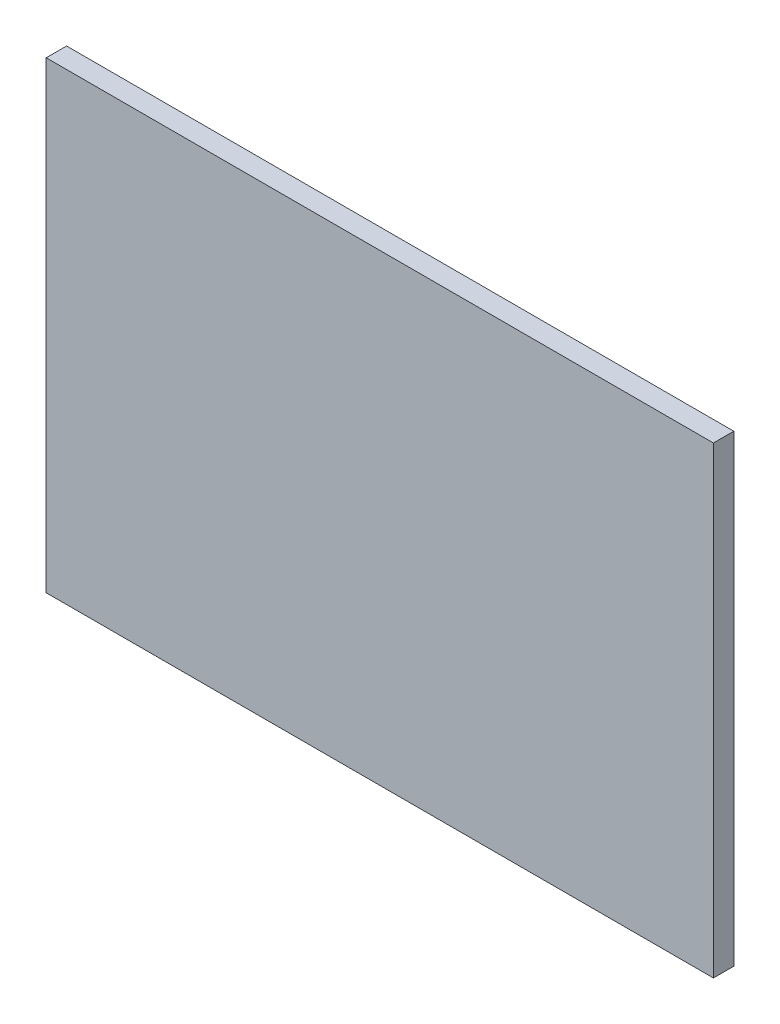
SolidWorks part; units mm, degrees
ref_plane "前视基准面" through (0, 0, 0) normal (0, 0, 1) x (1, 0, 0)
ref_plane "上视基准面" through (0, 0, 0) normal (0, 1, 0) x (1, 0, 0)
ref_plane "右视基准面" through (0, 0, 0) normal (1, 0, 0) x (0, 0, -1)
sketch "草图1" plane through (0, 0, 0) normal (0, 0, 1) x (1, 0, 0)
  line L1 (-18, -12.5) -> (18, -12.5)
  line L2 (-18, -12.5) -> (-18, 12.5)
  line L3 (-18, 12.5) -> (18, 12.5)
  line L4 (18, -12.5) -> (18, 12.5)
  line L5 (-18, -12.5) -> (18, 12.5) construction
  line L6 (-18, 12.5) -> (18, -12.5) construction
  circle A0 centre (0, 0) radius 8.75 construction
  dimension "D1" = 17.5
  dimension "D2" = 25
  dimension "D3" = 36
extrude "凸台-拉伸1" add sketch "草图1" along normal blind 1.1
